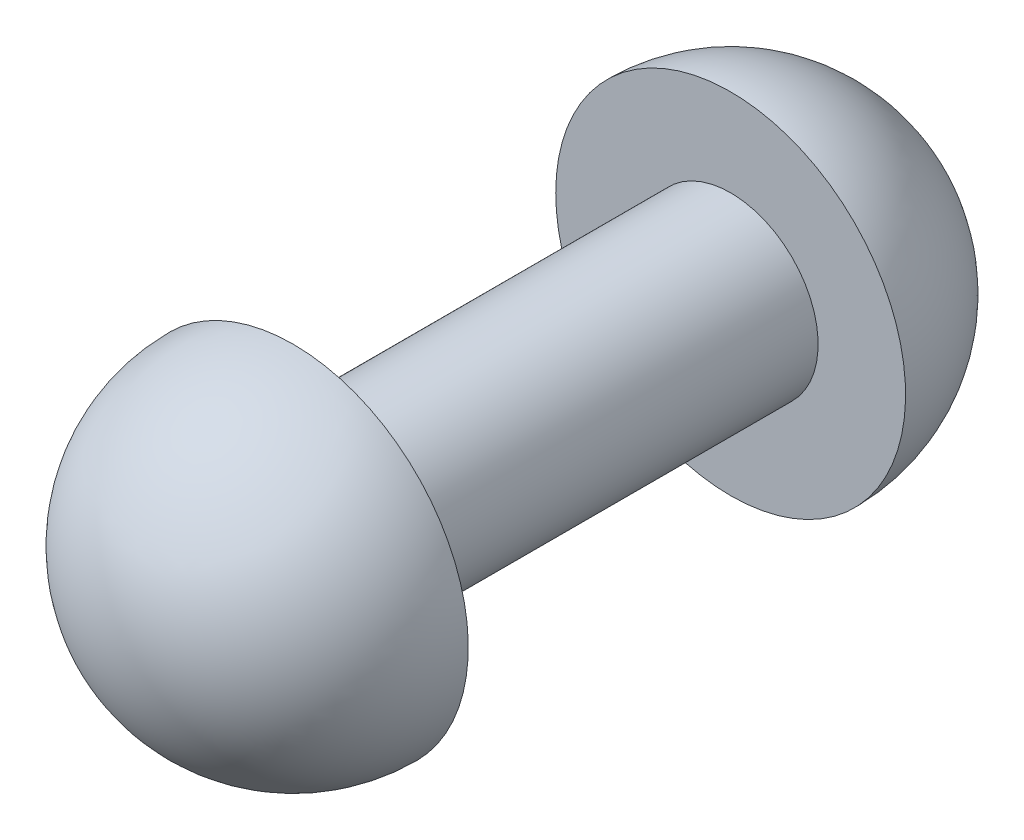
SolidWorks part; units mm, degrees
ref_plane "Front Plane" through (0, 0, 0) normal (0, 0, 1) x (1, 0, 0)
ref_plane "Top Plane" through (0, 0, 0) normal (0, 1, 0) x (1, 0, 0)
ref_plane "Right Plane" through (0, 0, 0) normal (1, 0, 0) x (0, 0, -1)
sketch "Sketch2" plane through (0, 0, 0) normal (1, 0, 0) x (0, 0, -1)
  line L0 (17.85, 0) -> (-16.725, 0) construction
  line L1 (-7.5, 3) -> (7.5, 3)
  line L2 (7.5, 3) -> (7.5, 6)
  line L3 (0, 0) -> (0, 11.8125) construction
  line L4 (-7.5, 3) -> (-7.5, 6)
  line L5 (-13.5, 0) -> (13.5, 0)
  arc A0 (7.5, 6) -> (13.5, 0) centre (7.5, 0) cw
  arc A1 (-7.5, 6) -> (-13.5, 0) centre (-7.5, 0) ccw
  dimension "D2" = 6
  dimension "D1" = 15
  dimension "D3" = 3
  dimension "D4" = 3
revolve "Revolve1" add sketch "Sketch2" angle 360 about L0
